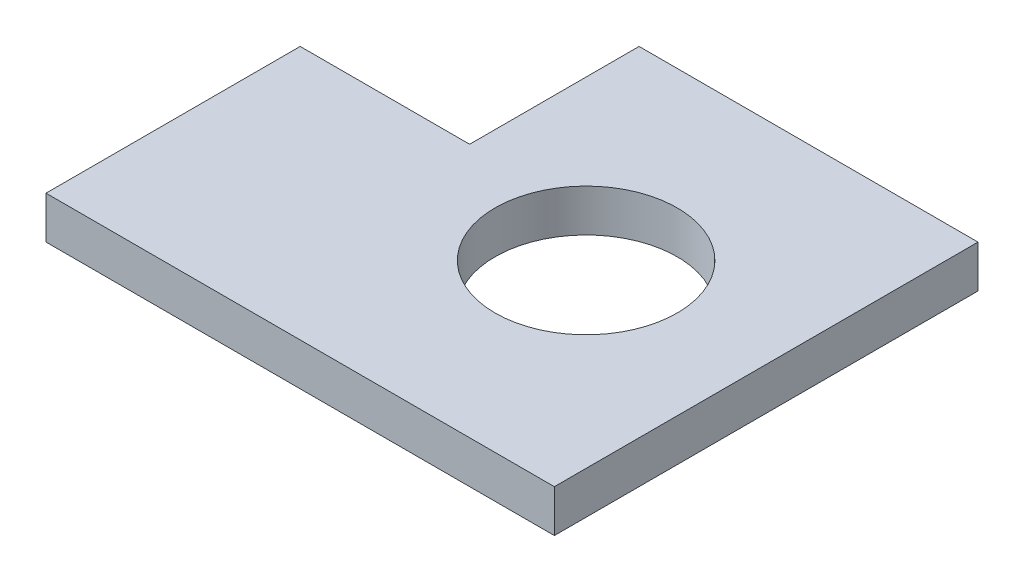
SolidWorks part; units mm, degrees
ref_plane "Спереди" through (0, 0, 0) normal (0, 0, 1) x (1, 0, 0)
ref_plane "Сверху" through (0, 0, 0) normal (0, 1, 0) x (1, 0, 0)
ref_plane "Справа" through (0, 0, 0) normal (1, 0, 0) x (0, 0, -1)
sketch "Эскиз1" plane through (0, 0, 0) normal (0, 1, 0) x (1, 0, 0)
  line L0 (0, 0) -> (120, 0)
  line L1 (120, 0) -> (120, 100)
  line L2 (120, 100) -> (40, 100)
  line L3 (40, 100) -> (40, 60)
  line L4 (40, 60) -> (0, 60)
  line L5 (0, 60) -> (0, 0)
  circle A0 centre (77.5, 50) radius 21.5
extrude "Бобышка-Вытянуть1" add sketch "Эскиз1" along normal blind 10
